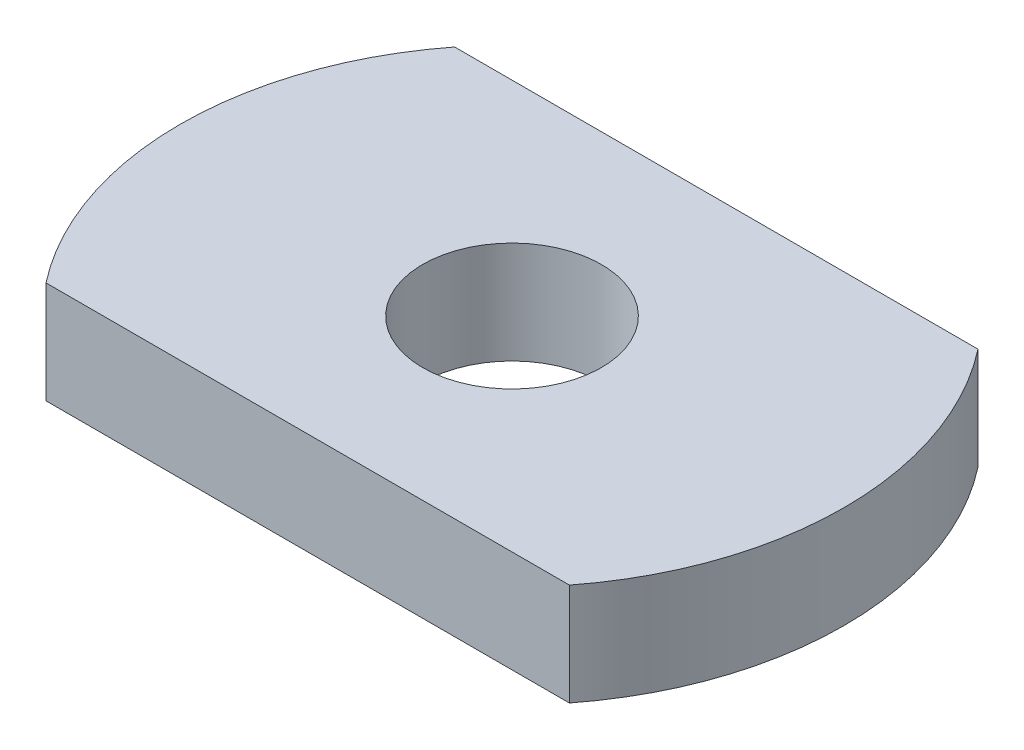
SolidWorks part; units mm, degrees
ref_plane "Front Plane" through (0, 0, 0) normal (0, 0, 1) x (1, 0, 0)
ref_plane "Top Plane" through (0, 0, 0) normal (0, 1, 0) x (1, 0, 0)
ref_plane "Right Plane" through (0, 0, 0) normal (1, 0, 0) x (0, 0, -1)
sketch "Sketch1" plane through (0, 0, 0) normal (0, 1, 0) x (1, 0, 0)
  line L1 (-10, 0) -> (-10, -4)
  line L2 (-10, 0) -> (10, 0)
  line L3 (0, 0) -> (0, 4)
  line L4 (-10, 4) -> (10, 4)
  line L5 (10, 0) -> (10, 4)
  line L6 (-10, 0) -> (10, 0)
  line L7 (0, 0) -> (0, -4)
  line L8 (-10, -4) -> (10, -4)
  line L9 (10, 0) -> (10, -4)
  line L10 (-10, 0) -> (-10, 4)
  circle A0 centre (0, 0) radius 6.5
  circle A1 centre (0, 0) radius 1.75
  dimension "D1" = 13
  dimension "D5" = 3.5
  dimension "D2" = 4
  dimension "D3" = 10
  dimension "D4" = 4
extrude "Boss-Extrude1" add sketch "Sketch1" along normal blind 2 contours A1 L3 L4 A0 L6 | A1 L6 A0 L8 L7 | A1 L6 A0 L4 L3 | A1 L7 L8 A0 L6
